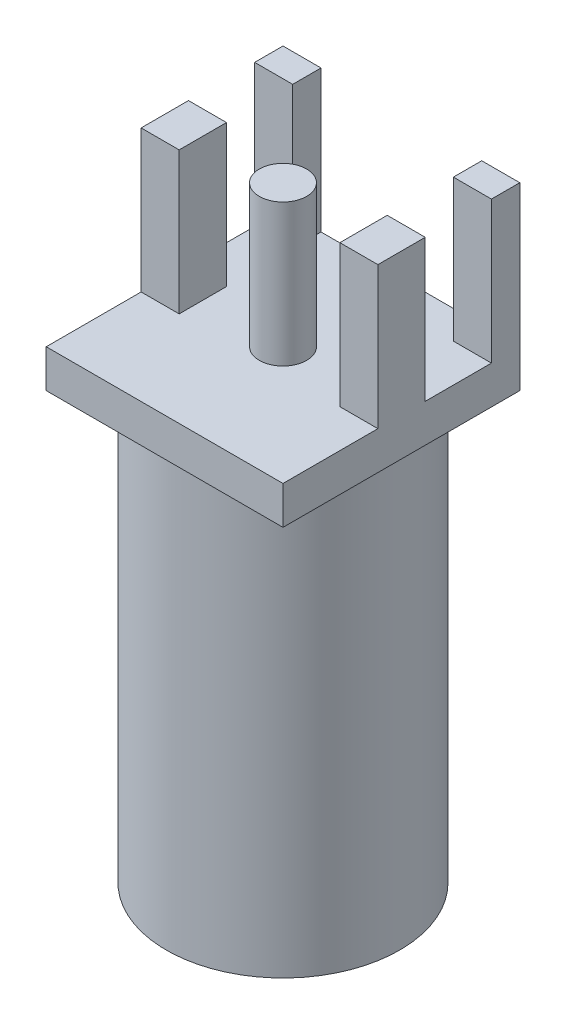
SolidWorks part; units mm, degrees
ref_plane "Front Plane" through (0, 0, 0) normal (0, 0, 1) x (1, 0, 0)
ref_plane "Top Plane" through (0, 0, 0) normal (0, 1, 0) x (1, 0, 0)
ref_plane "Right Plane" through (0, 0, 0) normal (1, 0, 0) x (0, 0, -1)
sketch "Sketch1" plane through (0, 0, 0) normal (0, 1, 0) x (1, 0, 0)
  line L1 (-3.175, 3.175) -> (3.175, 3.175)
  line L2 (-3.175, 3.175) -> (-3.175, -3.175)
  line L3 (-3.175, -3.175) -> (3.175, -3.175)
  line L4 (3.175, 3.175) -> (3.175, -3.175)
  line L5 (-3.175, 3.175) -> (3.175, -3.175) construction
  line L6 (-3.175, -3.175) -> (3.175, 3.175) construction
  point P0 (0, 0)
  dimension "D1" = 6.35
  dimension "D2" = 6.35
extrude "Boss-Extrude1" add sketch "Sketch1" along normal blind 1.02
sketch "Sketch2" plane through (0, 1.02, 0) normal (0, 1, 0) x (1, 0, 0)
  line L0 (-3.175, 3.175) -> (-3.175, -3.175) construction
  line L1 (-3.175, 3.175) -> (-2.155, 3.175)
  line L2 (-3.175, 3.175) -> (-3.175, 2.415)
  line L3 (-3.175, 2.415) -> (-2.155, 2.415)
  line L4 (-2.155, 3.175) -> (-2.155, 2.415)
  line L5 (-3.175, 0.64) -> (-2.155, 0.64)
  line L6 (-3.175, 0.64) -> (-3.175, -0.63)
  line L7 (-3.175, -0.63) -> (-2.155, -0.63)
  line L8 (-2.155, 0.64) -> (-2.155, -0.63)
  line L9 (0, 0) -> (0, -1.6462) construction
  line L10 (2.155, 0.64) -> (2.155, -0.63)
  line L11 (3.175, -0.63) -> (2.155, -0.63)
  line L12 (3.175, 0.64) -> (3.175, -0.63)
  line L13 (3.175, 0.64) -> (2.155, 0.64)
  line L14 (2.155, 3.175) -> (2.155, 2.415)
  line L15 (3.175, 2.415) -> (2.155, 2.415)
  line L16 (3.175, 3.175) -> (3.175, 2.415)
  line L17 (3.175, 3.175) -> (2.155, 3.175)
  dimension "D1" = 1.02
  dimension "D2" = 0.76
  dimension "D3" = 1.27
  dimension "D4" = 0.64
extrude "Boss-Extrude2" add sketch "Sketch2" along normal blind 3.81
sketch "Sketch3" plane through (0, 1.02, 0) normal (0, 1, 0) x (1, 0, 0)
  circle A0 centre (0, 0) radius 0.635
  dimension "D1" = 1.27
extrude "Boss-Extrude3" add sketch "Sketch3" along normal blind 3.81
sketch "Sketch4" plane through (0, 0, 0) normal (0, -1, 0) x (1, 0, 0)
  circle A0 centre (0, 0) radius 3.13
  dimension "D1" = 6.26
extrude "Boss-Extrude4" add sketch "Sketch4" along normal blind 11.43
